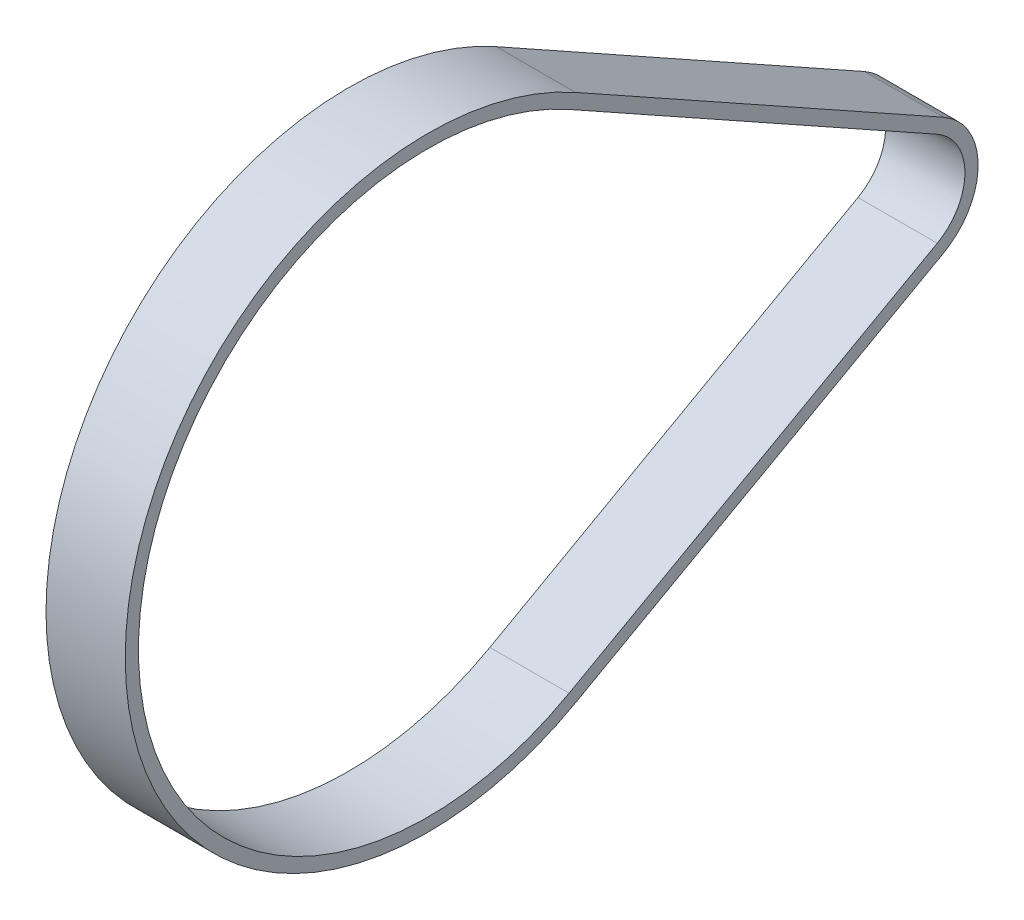
SolidWorks part; units mm, degrees
ref_plane "Front Plane" through (0, 0, 0) normal (0, 0, 1) x (1, 0, 0)
ref_plane "Top Plane" through (0, 0, 0) normal (0, 1, 0) x (1, 0, 0)
ref_plane "Right Plane" through (0, 0, 0) normal (1, 0, 0) x (0, 0, -1)
sketch "Sketch1" plane through (0, 0, 0) normal (1, 0, 0) x (0, 0, -1)
  line L0 (0, 37.672) -> (0, -29.9312) construction
  line L1 (-68.1193, 0) -> (49.7993, 0) construction
  line L2 (-17.7681, 50.0249) -> (51.9097, 11.1167)
  line L3 (-17.7681, -50.0249) -> (51.9097, -11.1167)
  line L4 (-45.7022, 57.2958) -> (-45.7022, 0) construction
  line L5 (-45.7022, 0) -> (-50.6958, 57.0778) construction
  line L6 (45.7022, 0) -> (57.4654, 4.8725) construction
  line L9 (-18.987, 47.8422) -> (50.6909, 8.9339)
  line L10 (-18.987, -47.8422) -> (50.6909, -8.9339)
  arc A0 (-17.7681, 50.0249) -> (-17.7681, -50.0249) centre (-45.7022, 0) ccw
  arc A1 (51.9097, -11.1167) -> (51.9097, 11.1167) centre (45.7022, 0) ccw
  arc A4 (50.6909, -8.9339) -> (50.6909, 8.9339) centre (45.7022, 0) ccw
  arc A5 (-18.987, 47.8422) -> (-18.987, -47.8422) centre (-45.7022, 0) ccw
  point P6 (85.003, 0)
  point P14 (-66.2011, 111.3818)
  dimension "D4" = 57.2958
  dimension "D5" = 12.7324
  dimension "D1" = 5
  dimension "D2" = 22.5
  dimension "D6" = 91.4044
  dimension "D7" = 2.5
extrude "Boss-Extrude1" add sketch "Sketch1" along normal mid plane 15
equation "\"D1@Sketch1\"=360/\"LARGE_TEETH\""
equation "\"D2@Sketch1\"=360/\"SMALL_TEETH\""
equation "\"LARGE_TEETH\"= 72"
equation "\"SMALL_TEETH\"= 16"
equation "\"BELT_LENGTH\"= 425mm"
equation "\"PITCH\"= 5mm"
equation "\"LARGE_C\"= \"LARGE_TEETH\" * \"PITCH\""
equation "\"SMALL_C\"= \"SMALL_TEETH\" * \"PITCH\""
equation "\"LARGE_RADIUS\"= \"LARGE_C\" / ( 2 * PI )"
equation "\"SMALL_RADIUS\"= \"SMALL_C\" / ( 2 * PI )"
equation "\"D4@Sketch1\"=\"LARGE_RADIUS\""
equation "\"D5@Sketch1\"=\"SMALL_RADIUS\""
equation "\"D3@Sketch1\"=\"BELT_LENGTH\""
